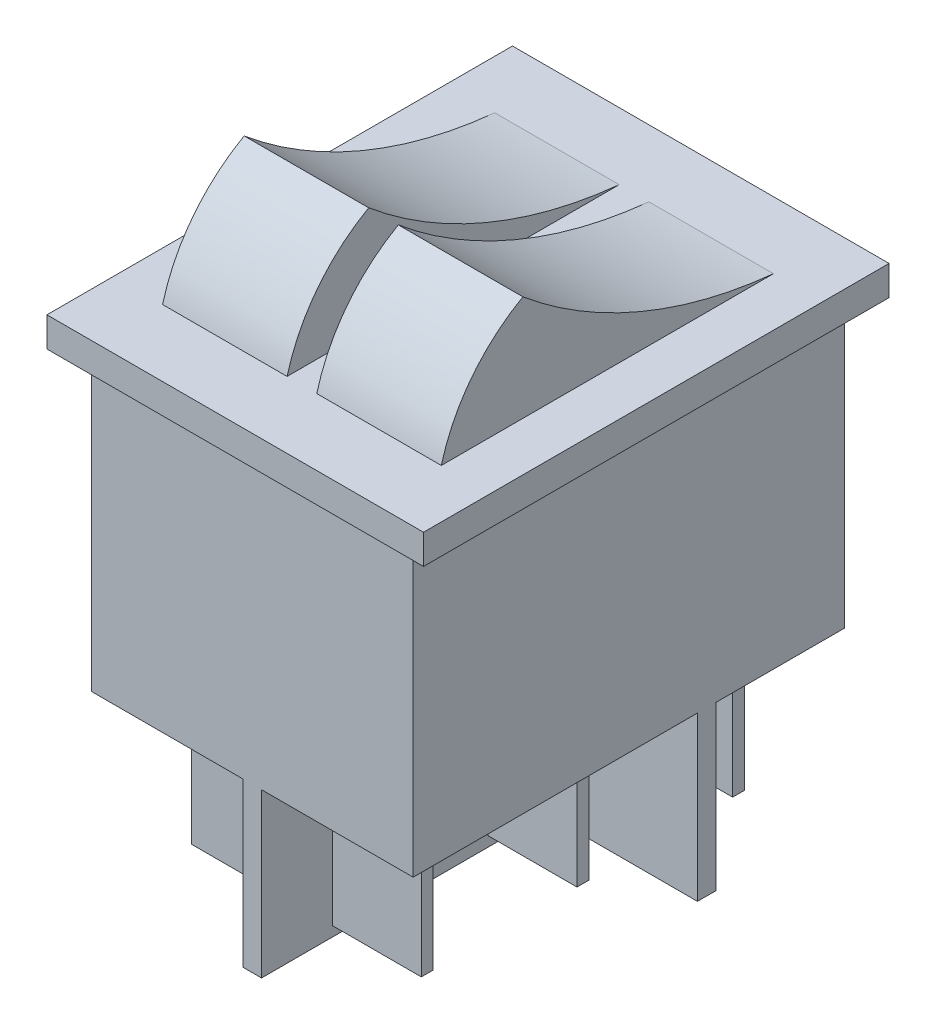
SolidWorks part; units mm, degrees
ref_plane "Alzado" through (0, 0, 0) normal (0, 0, 1) x (1, 0, 0)
ref_plane "Planta" through (0, 0, 0) normal (0, 1, 0) x (1, 0, 0)
ref_plane "Vista lateral" through (0, 0, 0) normal (1, 0, 0) x (0, 0, -1)
sketch "Croquis1" plane through (0, 0, 0) normal (0, 1, 0) x (1, 0, 0)
  line L1 (-12.7, 15.7) -> (12.7, 15.7)
  line L2 (-12.7, 15.7) -> (-12.7, -15.7)
  line L3 (-12.7, -15.7) -> (12.7, -15.7)
  line L4 (12.7, 15.7) -> (12.7, -15.7)
  line L5 (-12.7, 15.7) -> (12.7, -15.7) construction
  line L6 (-12.7, -15.7) -> (12.7, 15.7) construction
  point P0 (0, 0)
  dimension "D1" = 25.4
  dimension "D2" = 31.4
extrude "Saliente-Extruir1" add sketch "Croquis1" along normal blind 2
sketch "Croquis2" plane through (0, 0, 0) normal (1, 0, 0) x (0, 0, -1)
  line L0 (-15.7, 2) -> (15.7, 2) construction
  line L1 (-15.7, 2) -> (-15.7, 0) construction
  line L2 (0, 0) -> (0, 50000) construction
  line L3 (15.7, 2) -> (15.7, 0) construction
  line L4 (-11.2, 2) -> (11.2, 2)
  arc A0 (-11.2, 2) -> (-5.7, 9.1) centre (0, -0.9958) cw
  arc A1 (-5.7, 9.1) -> (11.2, 2) centre (14.2788, 32.9918) ccw
  point P14 (0, 0)
  dimension "D1" = 4.5
  dimension "D2" = 7.1
  dimension "D3" = 4.5
  dimension "D4" = 10
extrude "Saliente-Extruir2" add sketch "Croquis2" along normal blind 8.4 from offset 1
mirror "Simetría1" about plane through (0, 0, 0) normal (1, 0, 0) of "Saliente-Extruir2"
sketch "Croquis3" plane through (0, 0, 0) normal (0, -1, 0) x (1, 0, 0)
  line L1 (-10.85, 14.55) -> (10.85, 14.55)
  line L2 (-10.85, 14.55) -> (-10.85, -14.55)
  line L3 (-10.85, -14.55) -> (10.85, -14.55)
  line L4 (10.85, 14.55) -> (10.85, -14.55)
  line L5 (-10.85, 14.55) -> (10.85, -14.55) construction
  line L6 (-10.85, -14.55) -> (10.85, 14.55) construction
  point P0 (0, 0)
  dimension "D1" = 21.7
  dimension "D2" = 29.1
extrude "Saliente-Extruir3" add sketch "Croquis3" along normal blind 19.65
sketch "Croquis4" plane through (0, -19.65, 0) normal (0, -1, 0) x (1, 0, 0)
  line L0 (0, 0) -> (0, 50000) construction
  line L1 (0, 0) -> (50000, 0) construction
  line L2 (-18.0867, 10.5) -> (49981.9133, 10.5) construction
  line L3 (-18.0023, -10.5) -> (49981.9977, -10.5) construction
  line L4 (-4.75, -17.7494) -> (-4.75, 49982.2506) construction
  line L5 (1.75, 10.9) -> (7.75, 10.9)
  line L6 (-7.75, 10.9) -> (-1.75, 10.9)
  line L7 (-7.75, 10.9) -> (-7.75, 10.1)
  line L8 (-7.75, 10.1) -> (-1.75, 10.1)
  line L9 (-1.75, 10.9) -> (-1.75, 10.1)
  line L10 (-7.75, 10.9) -> (-1.75, 10.1) construction
  line L11 (-7.75, 10.1) -> (-1.75, 10.9) construction
  line L12 (1.75, 10.9) -> (1.75, 10.1)
  line L13 (1.75, 10.1) -> (7.75, 10.1)
  line L14 (7.75, 10.9) -> (7.75, 10.1)
  line L15 (1.75, 10.9) -> (7.75, 10.1) construction
  line L16 (1.75, 10.1) -> (7.75, 10.9) construction
  line L17 (1.75, 0.4) -> (7.75, 0.4)
  line L18 (1.75, 0.4) -> (1.75, -0.4)
  line L19 (1.75, -0.4) -> (7.75, -0.4)
  line L20 (7.75, 0.4) -> (7.75, -0.4)
  line L21 (1.75, 0.4) -> (7.75, -0.4) construction
  line L22 (1.75, -0.4) -> (7.75, 0.4) construction
  line L23 (1.75, -10.1) -> (7.75, -10.1)
  line L24 (1.75, -10.1) -> (1.75, -10.9)
  line L25 (1.75, -10.9) -> (7.75, -10.9)
  line L26 (7.75, -10.1) -> (7.75, -10.9)
  line L27 (1.75, -10.1) -> (7.75, -10.9) construction
  line L28 (1.75, -10.9) -> (7.75, -10.1) construction
  line L29 (-7.75, 0.4) -> (-1.75, 0.4)
  line L30 (-7.75, 0.4) -> (-7.75, -0.4)
  line L31 (-7.75, -0.4) -> (-1.75, -0.4)
  line L32 (-1.75, 0.4) -> (-1.75, -0.4)
  line L33 (-7.75, 0.4) -> (-1.75, -0.4) construction
  line L34 (-7.75, -0.4) -> (-1.75, 0.4) construction
  line L35 (-7.75, -10.1) -> (-1.75, -10.1)
  line L36 (-7.75, -10.1) -> (-7.75, -10.9)
  line L37 (-7.75, -10.9) -> (-1.75, -10.9)
  line L38 (-1.75, -10.1) -> (-1.75, -10.9)
  line L39 (-7.75, -10.1) -> (-1.75, -10.9) construction
  line L40 (-7.75, -10.9) -> (-1.75, -10.1) construction
  point P11 (-4.75, 10.5)
  point P16 (4.75, 10.5)
  point P23 (4.75, 0)
  point P28 (4.75, -10.5)
  point P33 (-4.75, 0)
  point P38 (-4.75, -10.5)
  dimension "D1" = 10.5
  dimension "D2" = 10.5
  dimension "D3" = 4.75
  dimension "D4" = 0.8
  dimension "D5" = 6
  dimension "D6" = 2
  dimension "D7" = 3
extrude "Saliente-Extruir4" add sketch "Croquis4" along normal blind 9.2
sketch "Croquis5" plane through (0, -19.65, 0) normal (0, -1, 0) x (1, 0, 0)
  line L0 (0, 0) -> (0, 50000) construction
  line L1 (-7.75, -0.4) -> (7.75, -10.1) construction
  line L2 (0, -5.25) -> (50000, -5.25) construction
  line L3 (0.625, 14.55) -> (-0.625, 14.55)
  line L4 (10.85, 14.55) -> (-10.85, 14.55) construction
  line L5 (-0.625, 14.55) -> (-0.625, -4.625)
  line L6 (-0.625, -4.625) -> (-10.85, -4.625)
  line L7 (-10.85, -4.625) -> (-10.85, -5.875)
  line L8 (-10.85, -5.875) -> (-0.625, -5.875)
  line L9 (-0.625, -5.875) -> (-0.625, -14.55)
  line L10 (-10.85, -14.55) -> (10.85, -14.55) construction
  line L11 (-0.625, -14.55) -> (0.625, -14.55)
  line L12 (-10.85, -14.55) -> (10.85, -14.55) construction
  line L14 (-10.85, 14.55) -> (-10.85, -14.55) construction
  line L15 (0.625, -5.875) -> (0.625, -14.55)
  line L16 (10.85, -5.875) -> (0.625, -5.875)
  line L17 (10.85, -4.625) -> (10.85, -5.875)
  line L18 (0.625, -4.625) -> (10.85, -4.625)
  line L19 (0.625, 14.55) -> (0.625, -4.625)
  point P9 (0, -5.25)
  point P12 (-10.85, -5.875)
  point P28 (0, -14.55)
  point P33 (0, 14.55)
  dimension "D1" = 1.25
  dimension "D2" = 1.25
  dimension "D3" = 1.25
extrude "Saliente-Extruir5" add sketch "Croquis5" along normal blind 11
